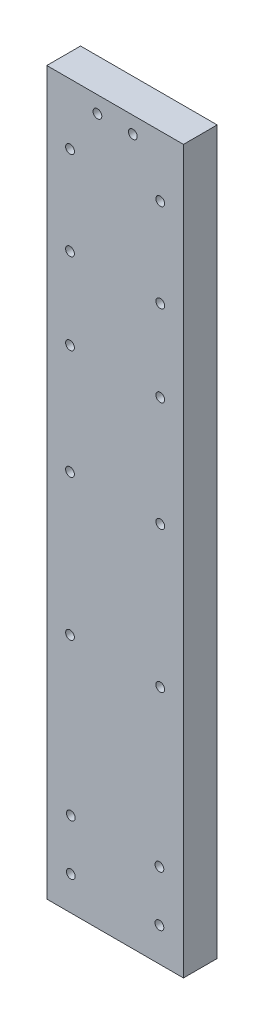
SolidWorks part; units mm, degrees
ref_plane "Front Plane" through (0, 0, 0) normal (0, 0, 1) x (1, 0, 0)
ref_plane "Top Plane" through (0, 0, 0) normal (0, 1, 0) x (1, 0, 0)
ref_plane "Right Plane" through (0, 0, 0) normal (1, 0, 0) x (0, 0, -1)
sketch "Sketch1" plane through (0, 0, 0) normal (0, 0, 1) x (1, 0, 0)
  line L0 (0, 0) -> (0, 85.59)
  line L1 (16.2, 0) -> (16.2, 85.59)
  line L2 (0, 47.74) -> (16.2, 47.74) construction
  line L3 (0, 0) -> (16.2, 0)
  line L4 (0, 14) -> (16.2, 14) construction
  line L5 (0, 26) -> (16.2, 26) construction
  line L6 (16.2, 85.59) -> (0, 85.59)
  line L7 (0, 70.385) -> (16.2, 70.385) construction
  line L8 (0, 55.74) -> (16.2, 55.74) construction
  line L10 (0, 76.385) -> (16.2, 76.385) construction
  circle A0 centre (13.45, 45.24) radius 0.52
  circle A1 centre (2.75, 67.885) radius 0.52
  circle A2 centre (13.45, 58.24) radius 0.52
  circle A3 centre (13.45, 78.385) radius 0.52
  circle A4 centre (2.75, 28.5) radius 0.52
  circle A5 centre (2.75, 78.385) radius 0.52
  circle A6 centre (2.75, 58.24) radius 0.52
  circle A7 centre (2.85, 10) radius 0.52
  circle A8 centre (13.35, 10) radius 0.52
  circle A9 centre (13.35, 4) radius 0.52
  circle A10 centre (2.85, 4) radius 0.52
  circle A11 centre (6, 83.635) radius 0.52
  circle A12 centre (13.45, 28.5) radius 0.52
  circle A13 centre (13.45, 67.885) radius 0.52
  circle A14 centre (10.2, 83.635) radius 0.52
  circle A15 centre (2.75, 45.24) radius 0.52
  dimension "D1" = 4
  dimension "D2" = 4
  dimension "D3" = 6
  dimension "D4" = 6
  dimension "D5" = 4
  dimension "D6" = 12
  dimension "D7" = 2.85
  dimension "D8" = 2.85
  dimension "D9" = 2.85
  dimension "D10" = 16.2
  dimension "D11" = 21.74
  dimension "D12" = 2.75
  dimension "D13" = 2.75
  dimension "D14" = 2.75
  dimension "D15" = 2.75
  dimension "D16" = 2.5
  dimension "D17" = 2.5
  dimension "D18" = 2.5
  dimension "D19" = 2.5
  dimension "D20" = 8
  dimension "D21" = 14.645
  dimension "D22" = 2.75
  dimension "D23" = 2.75
  dimension "D24" = 2.5
  dimension "D25" = 2.5
  dimension "D26" = 2.5
  dimension "D27" = 2.5
  dimension "D28" = 2.75
  dimension "D29" = 2.75
  dimension "D30" = 6
  dimension "D31" = 9.205
  dimension "D32" = 2.75
  dimension "D33" = 6
  dimension "D34" = 2
  dimension "D35" = 7.25
  dimension "D36" = 2
  dimension "D37" = 7.25
  dimension "D38" = 6
  dimension "D39" = 2.75
extrude "Boss-Extrude1" add sketch "Sketch1" along normal blind 4
equation "\"D11@Sketch1\"= \"HL@parametersSketch@prostheticParameters.SLDPRT\" * 0.204 - 4 - 12 'Pinky PIP Length"
equation "\"D21@Sketch1\"= \"HL@parametersSketch@prostheticParameters.SLDPRT\" * 0.117 - 4 - 3 'Pinky MIP Length"
equation "\"D31@Sketch1\"= \"HL@parametersSketch@prostheticParameters.SLDPRT\" * 0.093 - 3 - 5'Pinky DIP Length"
equation "\"D10@Sketch1\"= \"fingerWidth@parametersSketch@prostheticParameters.SLDPRT\"'Pinky Width"
